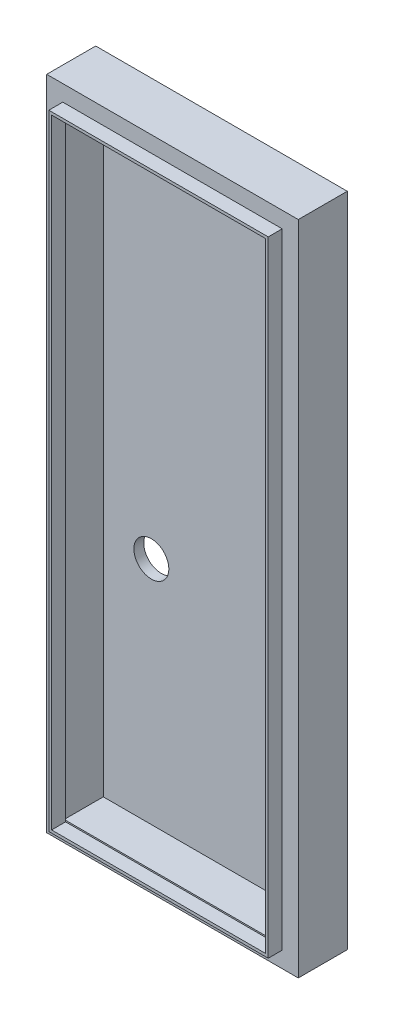
SolidWorks part; units mm, degrees
ref_plane "Front Plane" through (0, 0, 0) normal (0, 0, 1) x (1, 0, 0)
ref_plane "Top Plane" through (0, 0, 0) normal (0, 1, 0) x (1, 0, 0)
ref_plane "Right Plane" through (0, 0, 0) normal (1, 0, 0) x (0, 0, -1)
sketch "Sketch1" plane through (0, 0, 0) normal (0, 0, 1) x (1, 0, 0)
  line L1 (-87.4052, 75.6736) -> (-41.6852, 75.6736)
  line L2 (-87.4052, 75.6736) -> (-87.4052, -43.7064)
  line L3 (-87.4052, -43.7064) -> (-41.6852, -43.7064)
  line L4 (-41.6852, 75.6736) -> (-41.6852, -43.7064)
  line L5 (-84.4842, 72.6256) -> (-44.6062, 72.6256)
  line L6 (-84.4842, 72.6256) -> (-84.4842, -40.6584)
  line L7 (-84.4842, -40.6584) -> (-44.6062, -40.6584)
  line L8 (-44.6062, 72.6256) -> (-44.6062, -40.6584)
  line L9 (-83.9762, 72.1176) -> (-45.1142, 72.1176)
  line L10 (-83.9762, 72.1176) -> (-83.9762, -40.1504)
  line L11 (-83.9762, -40.1504) -> (-45.1142, -40.1504)
  line L12 (-45.1142, 72.1176) -> (-45.1142, -40.1504)
  dimension "D1" = 119.38
  dimension "D2" = 45.72
  dimension "D3" = 2.921
  dimension "D4" = 2.921
  dimension "D5" = 3.048
  dimension "D6" = 3.048
  dimension "D7" = 0.508
  dimension "D8" = 0.508
  dimension "D9" = 0.508
  dimension "D10" = 0.508
extrude "Boss-Extrude1" add sketch "Sketch1" along normal blind 1.27 and the other way blind 7.6368 contours L2 L3 L4 L1
sketch "Sketch2" plane through (0, 0, 1.27) normal (0, 0, 1) x (1, 0, 0)
  line L0 (-87.4052, 75.6736) -> (-41.6852, 75.6736) construction
  line L1 (-84.4842, 72.7526) -> (-44.6062, 72.7526)
  line L2 (-84.4842, 72.7526) -> (-84.4842, -40.7854)
  line L3 (-84.4842, -40.7854) -> (-44.6062, -40.7854)
  line L4 (-44.6062, 72.7526) -> (-44.6062, -40.7854)
  line L5 (-41.6852, 75.6736) -> (-41.6852, -43.7064) construction
  line L6 (-87.4052, -43.7064) -> (-41.6852, -43.7064) construction
  line L7 (-87.4052, 75.6736) -> (-87.4052, -43.7064) construction
  line L9 (-83.9762, 72.2446) -> (-45.1142, 72.2446)
  line L10 (-83.9762, 72.2446) -> (-83.9762, -40.2774)
  line L11 (-83.9762, -40.2774) -> (-45.1142, -40.2774)
  line L12 (-45.1142, 72.2446) -> (-45.1142, -40.2774)
  dimension "D1" = 2.921
  dimension "D2" = 2.921
  dimension "D3" = 2.921
  dimension "D4" = 2.921
  dimension "D5" = 0.508
  dimension "D6" = 0.508
  dimension "D7" = 0.508
  dimension "D8" = 0.508
extrude "Boss-Extrude2" add sketch "Sketch2" along normal blind 2.54
sketch "Sketch4" plane through (0, 0, -7.6368) normal (0, 0, -1) x (-1, 0, 0)
  line L0 (87.4052, 75.6736) -> (87.4052, -43.7064) construction
  line L1 (87.4052, -43.7064) -> (41.6852, -43.7064) construction
  circle A0 centre (75.5002, 1.7926) radius 3.175
  dimension "D1" = 6.35
  dimension "D2" = 11.905
  dimension "D3" = 45.499
extrude "Cut-Extrude1" cut sketch "Sketch4" against normal through all
sketch "Sketch5" plane through (0, 0, 1.27) normal (0, 0, 1) x (1, 0, 0)
sketch "Sketch12" plane through (0, 0, 1.27) normal (0, 0, 1) x (1, 0, 0)
  line L0 (-45.1142, -40.2774) -> (-45.1142, 72.2446) construction
  line L1 (-84.2302, 72.4986) -> (-44.8602, 72.4986)
  line L2 (-84.2302, 72.4986) -> (-84.2302, -40.0234)
  line L3 (-84.2302, -40.0234) -> (-44.8602, -40.0234)
  line L4 (-44.8602, 72.4986) -> (-44.8602, -40.0234)
  line L5 (-83.9762, -40.2774) -> (-45.1142, -40.2774) construction
  line L6 (-84.4842, 72.7526) -> (-84.4842, -40.7854) construction
  line L7 (-45.1142, 72.2446) -> (-83.9762, 72.2446) construction
  dimension "D1" = 0.254
  dimension "D2" = 0.254
  dimension "D3" = 0.254
  dimension "D4" = 0.254
extrude "Cut-Extrude3" cut sketch "Sketch12" against normal blind 7.112
